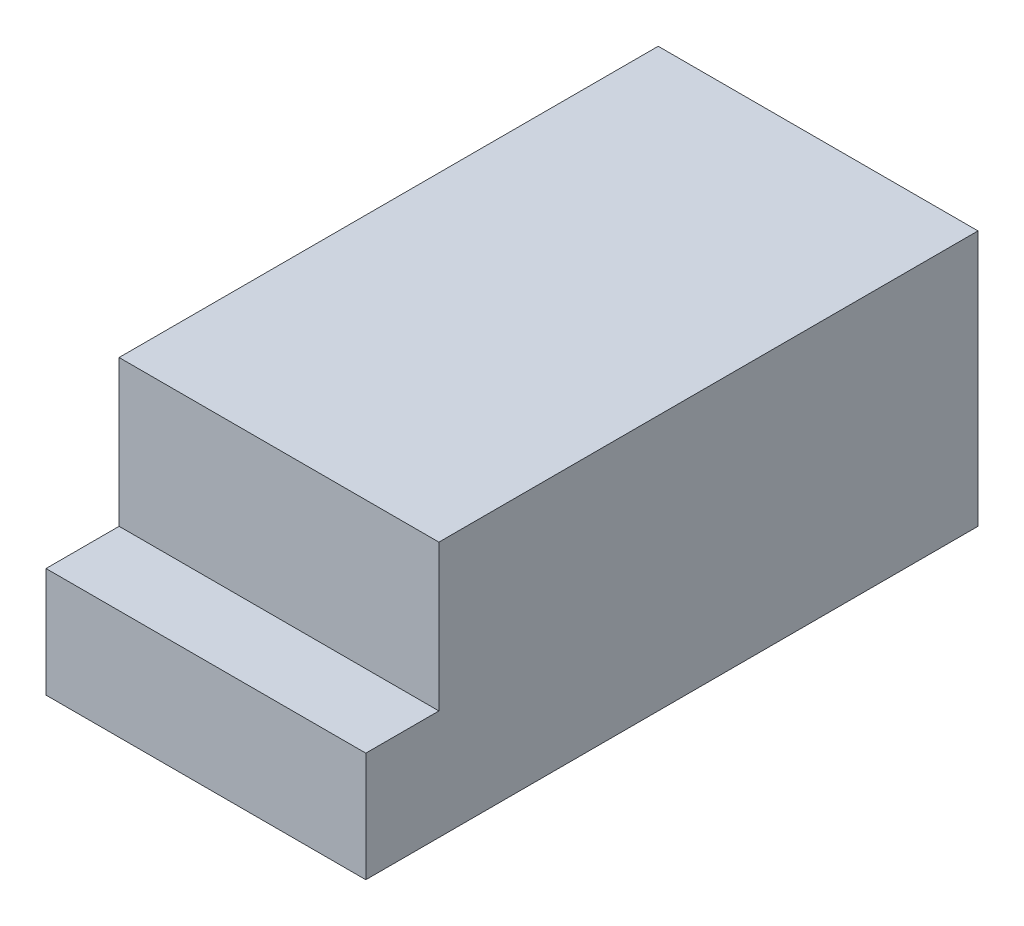
SolidWorks part; units mm, degrees
ref_plane "Front Plane" through (0, 0, 0) normal (0, 0, 1) x (1, 0, 0)
ref_plane "Top Plane" through (0, 0, 0) normal (0, 1, 0) x (1, 0, 0)
ref_plane "Right Plane" through (0, 0, 0) normal (1, 0, 0) x (0, 0, -1)
sketch "Sketch2" plane through (0, 0, 0) normal (0, 0, 1) x (1, 0, 0)
  line L1 (55.5625, -44.45) -> (-55.5625, -44.45)
  line L2 (55.5625, -44.45) -> (55.5625, 44.45)
  line L3 (55.5625, 44.45) -> (-55.5625, 44.45)
  line L4 (-55.5625, -44.45) -> (-55.5625, 44.45)
  line L5 (55.5625, -44.45) -> (-55.5625, 44.45) construction
  line L6 (55.5625, 44.45) -> (-55.5625, -44.45) construction
  point P0 (0, 0)
  dimension "D1" = 88.9
  dimension "D2" = 111.125
extrude "Boss-Extrude1" add sketch "Sketch2" along normal blind 212.725
sketch "Sketch4" plane through (0, 0, 212.725) normal (0, 0, 1) x (1, 0, 0)
  line L0 (55.5625, -44.45) -> (55.5625, 44.45) construction
  line L1 (-55.5625, 44.45) -> (55.5625, 44.45)
  line L2 (-55.5625, 44.45) -> (-55.5625, -6.35)
  line L3 (-55.5625, -6.35) -> (55.5625, -6.35)
  line L4 (55.5625, 44.45) -> (55.5625, -6.35)
  line L5 (-55.5625, -44.45) -> (55.5625, -44.45) construction
  dimension "D1" = 38.1
extrude "Cut-Extrude1" cut sketch "Sketch4" against normal blind 25.4
